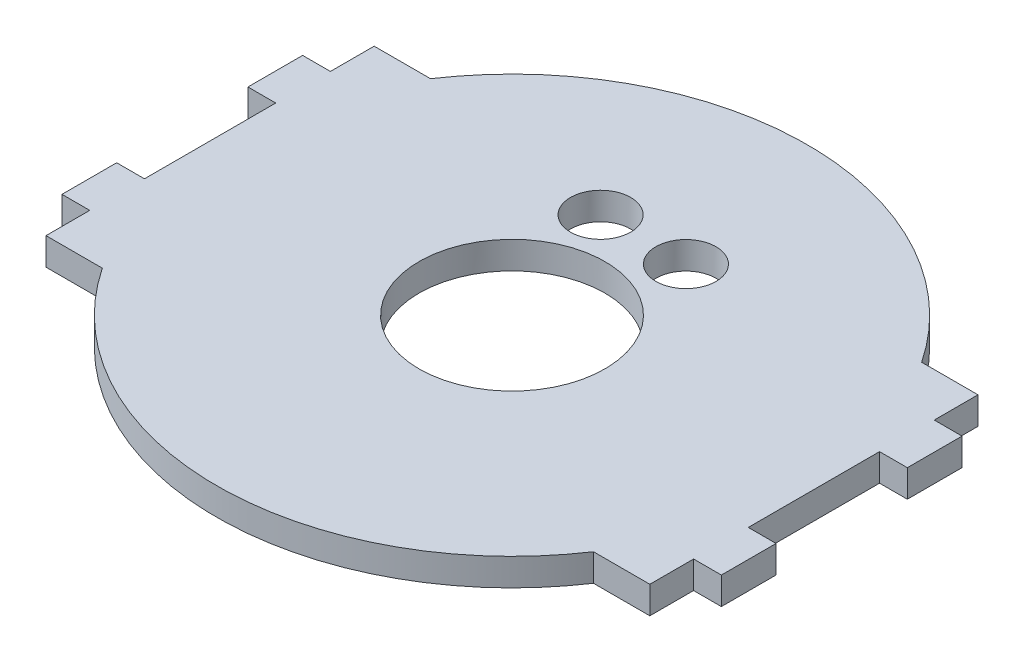
SolidWorks part; units mm, degrees
ref_plane "Front Plane" through (0, 0, 0) normal (0, 0, 1) x (1, 0, 0)
ref_plane "Top Plane" through (0, 0, 0) normal (0, 1, 0) x (1, 0, 0)
ref_plane "Right Plane" through (0, 0, 0) normal (1, 0, 0) x (0, 0, -1)
sketch "Sketch1" plane through (0, 0, 0) normal (0, 1, 0) x (1, 0, 0)
  line L1 (-35.052, -19.05) -> (35.052, -19.05)
  line L2 (-35.052, -19.05) -> (-35.052, 19.05)
  line L3 (-35.052, 19.05) -> (35.052, 19.05)
  line L4 (35.052, -19.05) -> (35.052, 19.05)
  line L5 (-35.052, -19.05) -> (35.052, 19.05) construction
  line L6 (-35.052, 19.05) -> (35.052, -19.05) construction
  point P0 (0, 0)
  dimension "D1" = 38.1
  dimension "D2" = 70.104
extrude "rectangular base" add sketch "Sketch1" along normal blind 3.175
sketch "Sketch2" plane through (0, 3.175, 0) normal (0, 1, 0) x (1, 0, 0)
  line L0 (0, 19.05) -> (0, 34.29) construction
  line L1 (35.052, 19.05) -> (-35.052, 19.05) construction
  line L2 (0, -19.05) -> (0, -35.56) construction
  line L3 (-35.052, -19.05) -> (35.052, -19.05) construction
  circle A2 centre (0, 0) radius 34.29
  dimension "D1" = 15.24
extrude "circular base add on" add sketch "Sketch2" against normal blind 3.175
sketch "Sketch4" plane through (0, 3.175, 0) normal (0, 1, 0) x (1, 0, 0)
  line L0 (-35.052, 0) -> (0, 0) construction
  line L2 (-35.052, 19.05) -> (-35.052, -19.05) construction
  line L3 (-35.052, 7.62) -> (-35.052, 13.97)
  line L4 (-35.052, 7.62) -> (-38.2778, 7.62)
  line L5 (-35.052, 13.97) -> (-38.2778, 13.97)
  line L6 (-38.2778, 7.62) -> (-38.2778, 13.97)
  line L7 (-35.052, -7.62) -> (-35.052, -13.97)
  line L8 (-35.052, -7.62) -> (-38.2778, -7.62)
  line L9 (-35.052, -13.97) -> (-38.2778, -13.97)
  line L10 (-38.2778, -7.62) -> (-38.2778, -13.97)
  dimension "D1" = 6.35
  dimension "D2" = 6.35
  dimension "D3" = 3.2258
  dimension "D4" = 3.2258
  dimension "D5" = 7.62
  dimension "D6" = 7.62
extrude "tab" add sketch "Sketch4" against normal blind 3.175
mirror "Mirror1" about plane through (0, 0, 0) normal (1, 0, 0) of "tab"
sketch "Sketch5" plane through (0, 3.175, 0) normal (0, 1, 0) x (1, 0, 0)
  circle A0 centre (0, 0) radius 3.556 construction
  circle A1 centre (0, 0) radius 10.795
  dimension "D1" = 21.59
extrude "Cut-Extrude1" cut sketch "Sketch5" against normal through all
sketch "Sketch6" plane through (0, 3.175, 0) normal (0, 1, 0) x (1, 0, 0)
  circle A0 centre (4.955, 15.24) radius 3.4925
  circle A1 centre (-4.955, 15.24) radius 3.4925
  dimension "D1" = 6.985
  dimension "D2" = 6.985
extrude "cut for screw access" cut sketch "Sketch6" against normal through all
